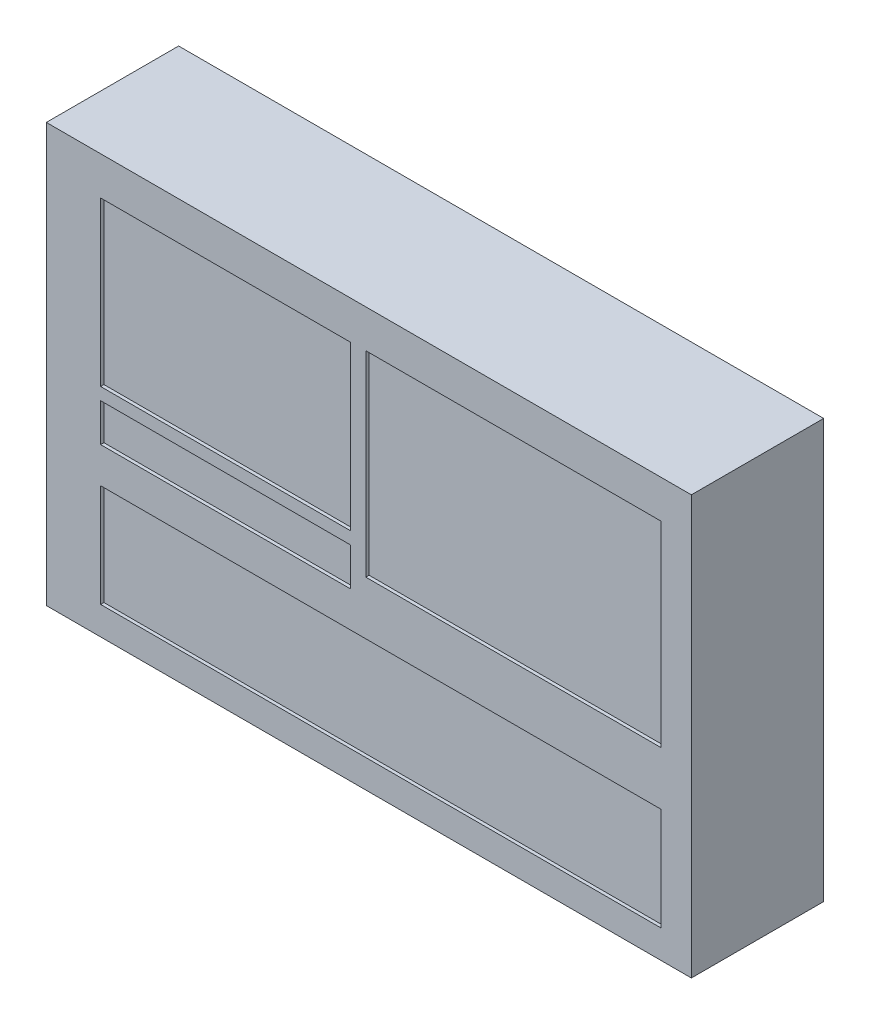
SolidWorks part; units mm, degrees
material "CA"
ref_plane "Front Plane" through (0, 0, 0) normal (0, 0, 1) x (1, 0, 0)
ref_plane "Top Plane" through (0, 0, 0) normal (0, 1, 0) x (1, 0, 0)
ref_plane "Right Plane" through (0, 0, 0) normal (1, 0, 0) x (0, 0, -1)
sketch "Sketch1" plane through (0, 0, 0) normal (0, 0, 1) x (1, 0, 0)
  line L1 (-272.3689, 127.4757) -> (117.6311, 127.4757)
  line L2 (-272.3689, 127.4757) -> (-272.3689, -125.5243)
  line L3 (-272.3689, -125.5243) -> (117.6311, -125.5243)
  line L4 (117.6311, 127.4757) -> (117.6311, -125.5243)
  dimension "D1" = 390
  dimension "D2" = 253
extrude "Boss-Extrude1" add sketch "Sketch1" along normal blind 80
sketch "Sketch2" plane through (0, 0, 80) normal (0, 0, 1) x (1, 0, 0)
  line L1 (-239.5445, 104.3302) -> (-88.3167, 104.3302)
  line L2 (-239.5445, 104.3302) -> (-239.5445, 5.6146)
  line L3 (-239.5445, 5.6146) -> (-88.3167, 5.6146)
  line L4 (-88.3167, 104.3302) -> (-88.3167, 5.6146)
  line L5 (-79.2245, 104.5158) -> (99.28, 104.5158)
  line L6 (-79.2245, 104.5158) -> (-79.2245, -14.0543)
  line L7 (-79.2245, -14.0543) -> (99.28, -14.0543)
  line L8 (99.28, 104.5158) -> (99.28, -14.0543)
  line L9 (-239.5445, -46.341) -> (99.28, -46.341)
  line L10 (-239.5445, -46.341) -> (-239.5445, -108.5021)
  line L11 (-239.5445, -108.5021) -> (99.28, -108.5021)
  line L12 (99.28, -46.341) -> (99.28, -108.5021)
  line L13 (-239.5445, -1.8076) -> (-88.3167, -1.8076)
  line L14 (-239.5445, -1.8076) -> (-239.5445, -24.8165)
  line L15 (-239.5445, -24.8165) -> (-88.3167, -24.8165)
  line L16 (-88.3167, -1.8076) -> (-88.3167, -24.8165)
extrude "Cut-Extrude1" cut sketch "Sketch2" against normal blind 2
